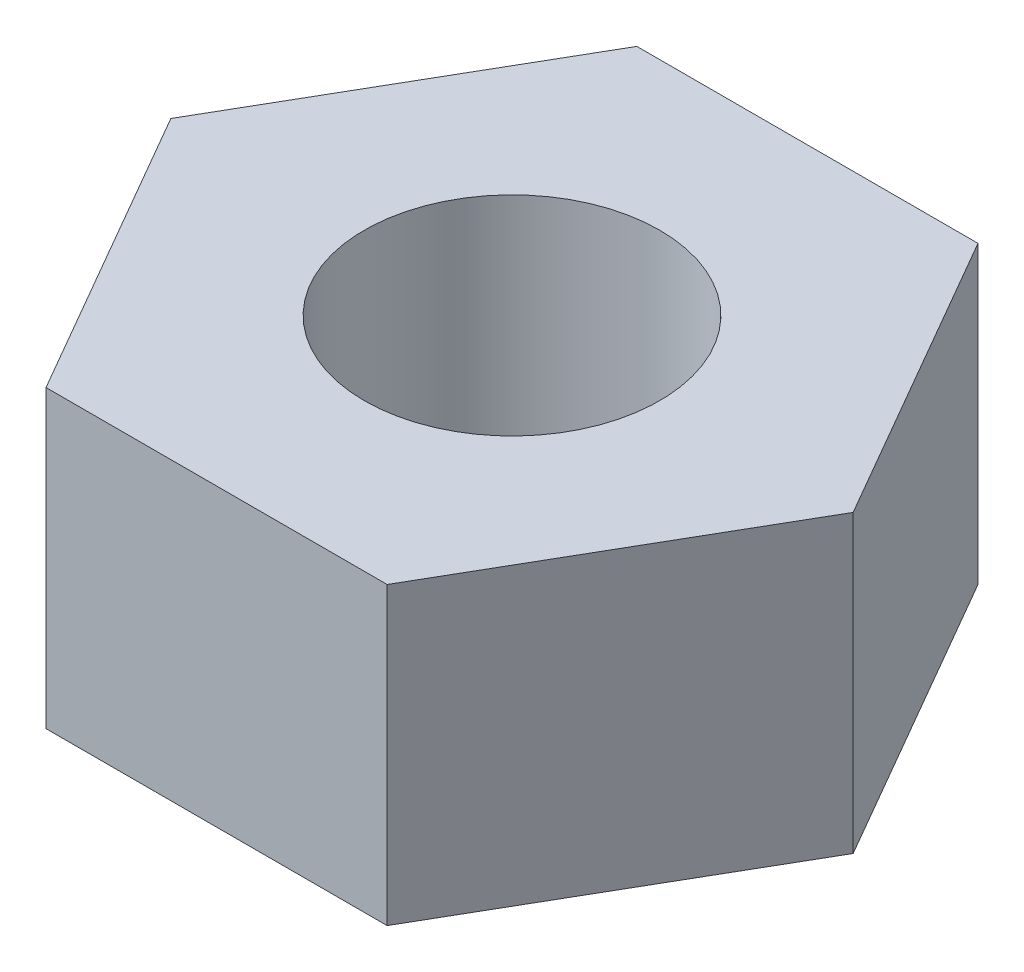
SolidWorks part; units mm, degrees
ref_plane "Front Plane" through (0, 0, 0) normal (0, 0, 1) x (1, 0, 0)
ref_plane "Top Plane" through (0, 0, 0) normal (0, 1, 0) x (1, 0, 0)
ref_plane "Right Plane" through (0, 0, 0) normal (1, 0, 0) x (0, 0, -1)
sketch "Sketch1" plane through (0, 0, 0) normal (0, 1, 0) x (1, 0, 0)
  line L1 (11.547, 0) -> (5.7735, 10)
  line L2 (5.7735, 10) -> (-5.7735, 10)
  line L3 (-5.7735, 10) -> (-11.547, 0)
  line L4 (-11.547, 0) -> (-5.7735, -10)
  line L5 (-5.7735, -10) -> (5.7735, -10)
  line L6 (5.7735, -10) -> (11.547, 0)
  circle A0 centre (0, 0) radius 5
  circle A1 centre (0, 0) radius 10 construction
  dimension "D1" = 10
  dimension "D2" = 20
extrude "Boss-Extrude1" add sketch "Sketch1" along normal blind 10
